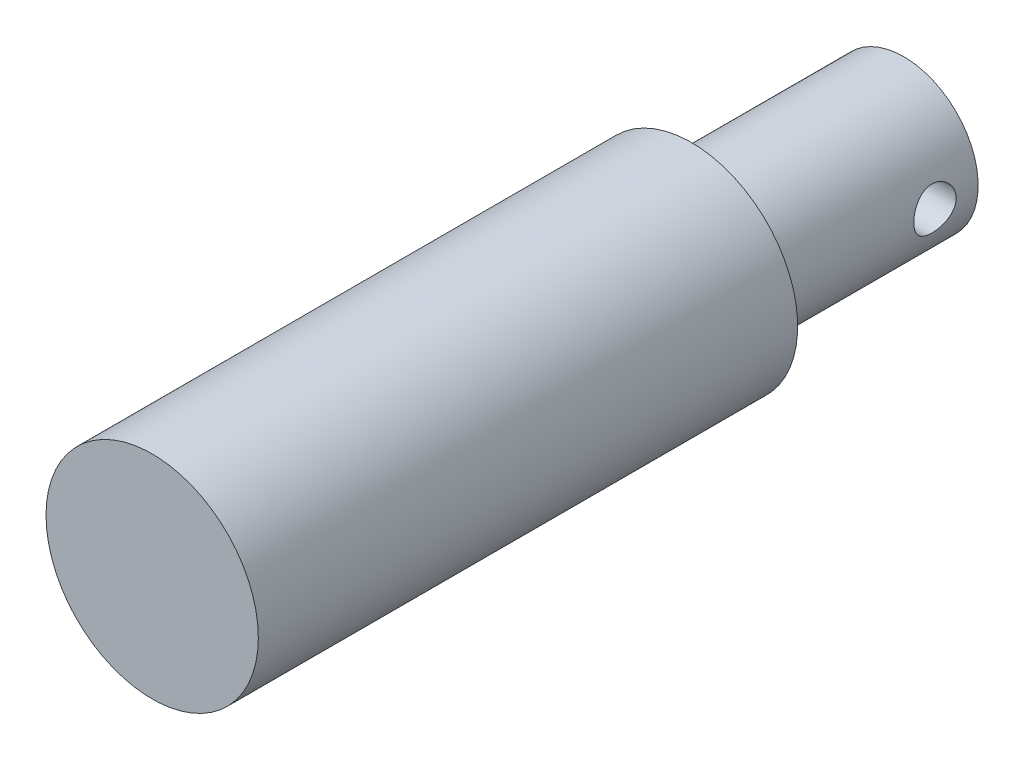
SolidWorks part; units mm, degrees
ref_plane "Front Plane" through (0, 0, 0) normal (0, 0, 1) x (1, 0, 0)
ref_plane "Top Plane" through (0, 0, 0) normal (0, 1, 0) x (1, 0, 0)
ref_plane "Right Plane" through (0, 0, 0) normal (1, 0, 0) x (0, 0, -1)
sketch "Sketch1" plane through (0, 0, 0) normal (0, 0, 1) x (1, 0, 0)
  circle A0 centre (0, 0) radius 5
extrude "Boss-Extrude1" add sketch "Sketch1" along normal blind 35.4
sketch "Sketch2" plane through (0, 0, 0) normal (1, 0, 0) x (0, 0, -1)
  circle A0 centre (-2.0314, 0) radius 1
extrude "Cut-Extrude1" cut sketch "Sketch2" against normal through all and the other way through all
sketch "Sketch3" plane through (0, 0, 0) normal (0, 0, -1) x (-1, 0, 0)
  circle A0 centre (0, 0) radius 3.5
  dimension "D1" = 7
extrude "Cut-Extrude2" cut sketch "Sketch3" against normal blind 10 flip side to cut
